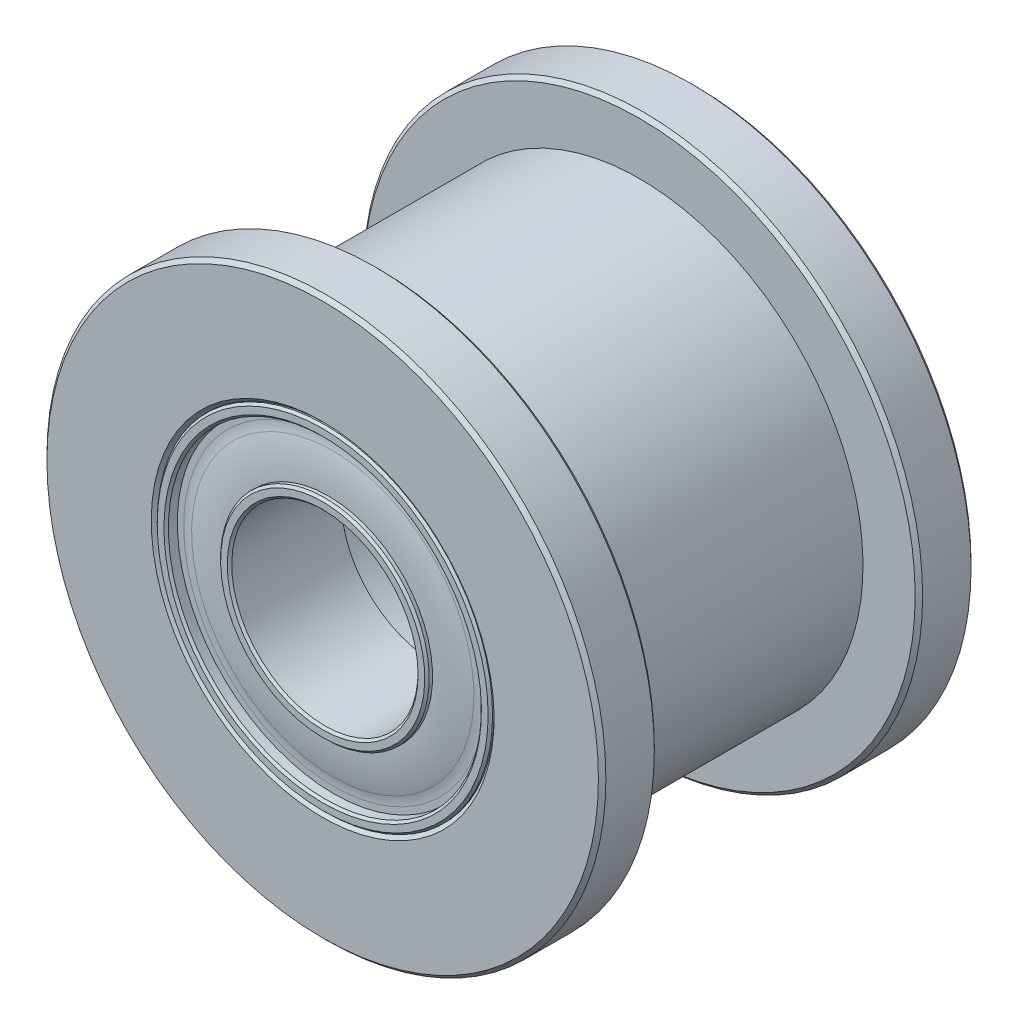
SolidWorks part; units mm, degrees
material "6061-T6 (SS)"
ref_plane "Front" through (0, 0, 0) normal (0, 0, 1) x (1, 0, 0)
ref_plane "Top" through (0, 0, 0) normal (0, 1, 0) x (1, 0, 0)
ref_plane "Right" through (0, 0, 0) normal (1, 0, 0) x (0, 0, -1)
sketch "Sketch1" plane through (0, 0, 0) normal (1, 0, 0) x (0, 0, -1)
  line L0 (-5, 0) -> (5, 0) construction
  line L1 (5, 7.5) -> (5, -7.5) construction
  line L2 (5, 7.5) -> (3.5, 7.5) construction
  line L3 (5, 2.5) -> (5, -2.5) construction
  line L4 (5, 6) -> (5, -6) construction
  line L5 (3, 0) -> (-3, 0) construction
  line L6 (3.5, 7.5) -> (3.5, 6) construction
  line L7 (5, 4.5) -> (2, 4.5) construction
  line L8 (2, 4.5) -> (2, 2.5) construction
  line L9 (2, 2.5) -> (5, 2.5) construction
  line L10 (5, 4.5) -> (5, -4.5) construction
  line L11 (-5, 0) -> (-5, 7.5) construction
  line L12 (-5, 7.5) -> (-3.5, 7.5) construction
  line L13 (-3.5, 7.5) -> (-3.5, 6) construction
  line L14 (-3.5, 6) -> (3.5, 6) construction
  line L15 (3.5, 6) -> (3.5, -6) construction
  line L16 (3.5, -6) -> (-3.5, -6) construction
  line L17 (-3.5, -6) -> (-3.5, 6) construction
  line L18 (0, -3.5) -> (0, 3.5) construction
  point P15 (5, 0)
  point P22 (3.5, 0)
  point P24 (-3, -6)
  point P25 (3, -6)
  point P29 (0, 0)
  dimension "Width" = 10
  dimension "OD" = 15
  dimension "ID" = 5
  dimension "Diameter" = 12
  dimension "Groove Depth" = 1.5
  dimension "For Maximum Belt Width" = 6
  dimension "For Shaft Diameter" = 5
  dimension "Bearing Diameter" = 9
  dimension "Bearing Width" = 3
  dimension "Inside Width" = 7
  dimension "Wall Thickness" = 1.5
  dimension "D1" = 7
sketch "Sketch5" plane through (0, 0, 0) normal (0, 0, 1) x (1, 0, 0)
  circle A0 centre (0, 0) radius 7.5 construction
  circle A1 centre (0, 0) radius 6 construction
  circle A2 centre (0, 0) radius 2.5 construction
  point P5 (0, 0)
  point P9 (-6, 0)
  point P10 (-7.5, 0)
  point P13 (0, 6)
sketch "Sketch2" plane through (0, 0, 0) normal (1, 0, 0) x (0, 0, -1)
  line L0 (5, 2.5) -> (2, 2.5)
  line L1 (5, 2.5) -> (5, 2.8)
  line L2 (5, 7.5) -> (5, -7.5) construction
  line L3 (5, 2.8) -> (4.7, 2.8) construction
  line L4 (4.85, 4.2) -> (4.85, 2.8) construction
  line L5 (5, 4.5) -> (2, 4.5)
  line L6 (4.7, 3.9) -> (4.7, 4.2)
  line L7 (5, 4.5) -> (5, 4.2)
  line L8 (5, 4.2) -> (4.7, 4.2)
  line L9 (4.7, 4.2) -> (4.7, 2.8) construction
  line L10 (2, 4.5) -> (2, 2.5)
  line L11 (4.85, 2.8) -> (5, 2.8)
  arc A0 (4.7, 3.9) -> (4.85, 2.8) centre (0.7417, 2.8) cw
  dimension "D1" = 0.3
revolve "Revolve1" add sketch "Sketch2" angle 360 about L0
chamfer "Chamfer2" distance 0.06 angle 45 4 edges at (0, -2.8, -5) (0, -2.5, -5) (0, -4.2, -5) (0, -4.5, -5)
fillet "Fillet2" radius 1 1 edges at (0, -3.9, -4.7)
mirror "Mirror1" about plane through (0, 0, 0) normal (0, 0, 1) of bodies 108
sketch "Sketch3" plane through (0, 0, 0) normal (1, 0, 0) x (0, 0, -1)
  line L0 (3.5, 7.5) -> (5, 7.5)
  line L1 (5, 7.5) -> (5, 4.5)
  line L2 (5, 7.5) -> (5, -7.5) construction
  line L3 (-5, 4.5) -> (-2, 4.5)
  line L4 (-2, 4.5) -> (-2, 3.5)
  line L5 (-2, 3.5) -> (2, 3.5)
  line L6 (2, 3.5) -> (2, 4.5)
  line L8 (2, 4.5) -> (5, 4.5)
  line L9 (3.5, 7.5) -> (3.5, 6)
  line L10 (3.5, 6) -> (-3.5, 6)
  line L11 (0, 6) -> (0, 4.5) construction
  line L12 (-5, 4.5) -> (5, 4.5) construction
  line L13 (-3.5, 7.5) -> (-3.5, 6)
  line L19 (-5, 7.5) -> (-5, 4.5)
  line L20 (-3.5, 7.5) -> (-5, 7.5)
revolve "Revolve2" add sketch "Sketch3" angle 360 about L0
chamfer "Chamfer1" distance 0.1 angle 45 6 edges at (0, -7.5, -5) (0, -7.5, -3.5) (0, -7.5, 3.5) (0, -7.5, 5) (0, -4.5, -5) (0, -4.5, 5)
equation "\"D1@Sketch1\"=\"ID@Sketch1\"+2"
